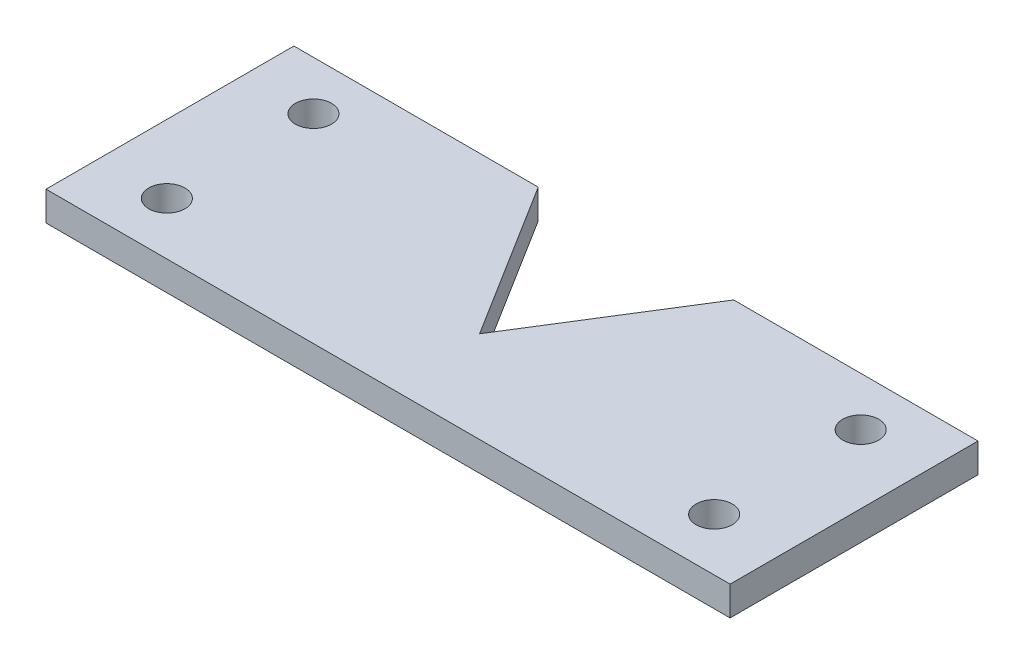
SolidWorks part; units mm, degrees
ref_plane "Ebene vorne" through (0, 0, 0) normal (0, 0, 1) x (1, 0, 0)
ref_plane "Ebene oben" through (0, 0, 0) normal (0, 1, 0) x (1, 0, 0)
ref_plane "Ebene rechts" through (0, 0, 0) normal (1, 0, 0) x (0, 0, -1)
sketch "Skizze1" plane through (0, 0, 0) normal (0, 0, 1) x (1, 0, 0)
  line L0 (-85.0721, 14.3687) -> (-15.0721, 14.3687)
  line L1 (-85.0721, 14.3687) -> (-85.0721, 34.3687)
  line L2 (-85.0721, 34.3687) -> (-65.8054, 34.3687)
  line L3 (-65.8054, 34.3687) -> (-65.8054, 28.3687)
  line L4 (-65.8054, 28.3687) -> (-34.3388, 28.3687)
  line L5 (-50.0721, 28.3687) -> (-50.0721, 14.3687)
  line L6 (-34.3388, 34.3687) -> (-34.3388, 28.3687)
  line L7 (-15.0721, 34.3687) -> (-34.3388, 34.3687)
  line L8 (-15.0721, 14.3687) -> (-15.0721, 34.3687)
  dimension "D1" = 20
  dimension "D2" = 70
  dimension "D3" = 6
extrude "Aufsatz-Linear austragen1" add sketch "Skizze1" along normal blind 40 contours L5 L4 L3 L2 L1 L0 | L0 L8 L7 L6 L4 L5
hole_wizard "Durchgangsloch für M81" positions "Skizze2" profile "Skizze3" hole size "M8" standard "ISO" end condition through all
sketch "Skizze2" plane through (0, 34.3687, 0) normal (0, 1, 0) x (1, 0, 0)
  line L0 (-85.0721, -40) -> (-85.0721, 0) construction
  line L1 (-85.0721, -40) -> (-65.8054, -40) construction
  line L2 (-15.0721, -40) -> (-15.0721, 0) construction
  line L3 (-15.0721, -40) -> (-34.3388, -40) construction
  point P0 (-78.0721, -33)
  point P2 (-22.0721, -33)
  dimension "D1" = 7
  dimension "D2" = 7
  dimension "D3" = 7
  dimension "D4" = 7
sketch "Skizze3" plane through (-78.0721, 34.3687, 33) normal (1, 0, 0) x (0, 0, 1)
  line L0 (0, 0) -> (0, 20)
  line L1 (0, 20) -> (4.2, 20)
  line L2 (4.2, 20) -> (4.2, 0)
  line L5 (4.2, 0) -> (0, 0)
  line L11 (0, -6.35) -> (0, 107.95) construction
  dimension "Bohrerdurchmesser" = 8.4
  dimension "Bohrungstiefe" = 20
hole_wizard "Durchgangsloch für M3.51" positions "Skizze16" profile "Skizze17" hole size "M3.5" standard "ISO" end condition through all
sketch "Skizze16" plane through (0, 34.3687, 0) normal (0, 1, 0) x (1, 0, 0)
  line L0 (-85.0721, -40) -> (-85.0721, 0) construction
  line L1 (-15.0721, -40) -> (-15.0721, 0) construction
  line L2 (-15.0721, 0) -> (-34.3388, 0) construction
  line L3 (-11, 0) -> (11, 0) construction
  point P0 (-78.0721, -5)
  point P2 (-78.0721, -20)
  point P4 (-22.0721, -20)
  point P6 (-22.0721, -5)
  dimension "D1" = 7
  dimension "D2" = 7
  dimension "D3" = 5
  dimension "D4" = 5
  dimension "D5" = 7
  dimension "D6" = 7
  dimension "D7" = 15
  dimension "D8" = 15
sketch "Skizze17" plane through (-78.0721, 34.3687, 5) normal (1, 0, 0) x (0, 0, 1)
  line L0 (0, 0) -> (0, 20)
  line L1 (0, 20) -> (1.85, 20)
  line L2 (1.85, 20) -> (1.85, 0)
  line L5 (1.85, 0) -> (0, 0)
  line L11 (0, -6.35) -> (0, 107.95) construction
  dimension "Bohrerdurchmesser" = 3.7
  dimension "Bohrungstiefe" = 20
sketch "Skizze18" plane through (0, 28.3687, 0) normal (0, 1, 0) x (1, 0, 0)
  line L0 (-15.0721, -40) -> (-15.0721, 0) construction
  line L1 (-65.8054, -40) -> (-34.3388, -40) construction
  circle A0 centre (-50.0721, -33) radius 4.8
  dimension "D1" = 35
  dimension "D2" = 7
hole_wizard "Durchgangsloch für M82" positions "Skizze19" profile "Skizze20" hole size "M8" standard "ISO" end condition through all
sketch "Skizze19" plane through (0, 14.3687, 0) normal (0, -1, 0) x (-1, 0, 0)
  line L0 (85.0721, -40) -> (85.0721, 0) construction
  line L1 (85.0721, -40) -> (15.0721, -40) construction
  point P0 (50.0721, -33)
  dimension "D1" = 35
  dimension "D2" = 7
sketch "Skizze20" plane through (-50.0721, 14.3687, 33) normal (1, 0, 0) x (0, 0, -1)
  line L0 (0, 0) -> (0, 20)
  line L1 (0, 20) -> (4.2, 20)
  line L2 (4.2, 20) -> (4.2, 0.025)
  line L3 (4.2, 0.025) -> (4.225, 0)
  line L5 (4.225, 0) -> (0, 0)
  line L6 (-4.2, 0.025) -> (-4.225, 0) construction
  line L11 (0, -6.35) -> (0, 107.95) construction
  dimension "Bohrerdurchmesser" = 8.4
  dimension "Bohrungstiefe" = 20
  dimension "Senkdurchmesser2 (Oben)" = 8.45
  dimension "Senkwinkel2 (Oben)" = 90
sketch "Skizze21" plane through (0, 28.3687, 0) normal (0, 1, 0) x (1, 0, 0)
  circle A0 centre (-50.0721, -33) radius 5
extrude "Schnitt-Linear austragen1" cut sketch "Skizze21" against normal blind 12
sketch "Skizze22" plane through (0, 34.3687, 0) normal (0, 1, 0) x (1, 0, 0)
  line L0 (-85.0721, -40) -> (-85.0721, 0) construction
  line L1 (-85.0721, -25.3665) -> (-15.0721, -25.3665)
  line L2 (-85.0721, -25.3665) -> (-85.0721, -40)
  line L3 (-85.0721, -40) -> (-15.0721, -40)
  line L4 (-15.0721, -25.3665) -> (-15.0721, -40)
extrude "Schnitt-Linear austragen2" cut sketch "Skizze22" against normal blind 20
sketch "Skizze23" plane through (0, 0, 0) normal (0, 0, -1) x (-1, 0, 0)
  line L0 (85.0721, 14.3687) -> (85.0721, 34.3687) construction
  line L1 (15.0721, 34.3687) -> (85.0721, 34.3687)
  line L2 (15.0721, 34.3687) -> (15.0721, 19.3687)
  line L3 (15.0721, 19.3687) -> (85.0721, 19.3687)
  line L4 (85.0721, 34.3687) -> (85.0721, 19.3687)
  dimension "D1" = 15
extrude "Schnitt-Linear austragen3" cut sketch "Skizze23" against normal blind 26
sketch "Skizze25" plane through (0, 0, 25.3665) normal (0, 0, 1) x (1, 0, 0)
  line L0 (-85.0721, 14.3687) -> (-85.0721, 19.3687) construction
  line L1 (-85.0721, 16.3687) -> (-15.0721, 16.3687)
  line L2 (-85.0721, 16.3687) -> (-85.0721, 14.3687)
  line L3 (-85.0721, 14.3687) -> (-15.0721, 14.3687)
  line L4 (-15.0721, 16.3687) -> (-15.0721, 14.3687)
  line L5 (-15.0721, 19.3687) -> (-85.0721, 19.3687) construction
  dimension "D1" = 3
extrude "Schnitt-Linear austragen5" cut sketch "Skizze25" against normal blind 26
sketch "Skizze26" plane through (0, 16.3687, 0) normal (0, -1, 0) x (1, 0, 0)
  line L0 (-40.0721, 0) -> (-50.0721, 16)
  line L1 (-50.0721, 16) -> (-60.0721, 0)
  line L2 (-60.0721, 0) -> (-40.0721, 0)
  line L3 (-85.0721, 0) -> (-85.0721, 25.3665) construction
  line L4 (-15.0721, 0) -> (-15.0721, 25.3665) construction
  dimension "D1" = 25
  dimension "D2" = 25
  dimension "D3" = 35
  dimension "D4" = 16
extrude "Schnitt-Linear austragen6" cut sketch "Skizze26" against normal blind 3
